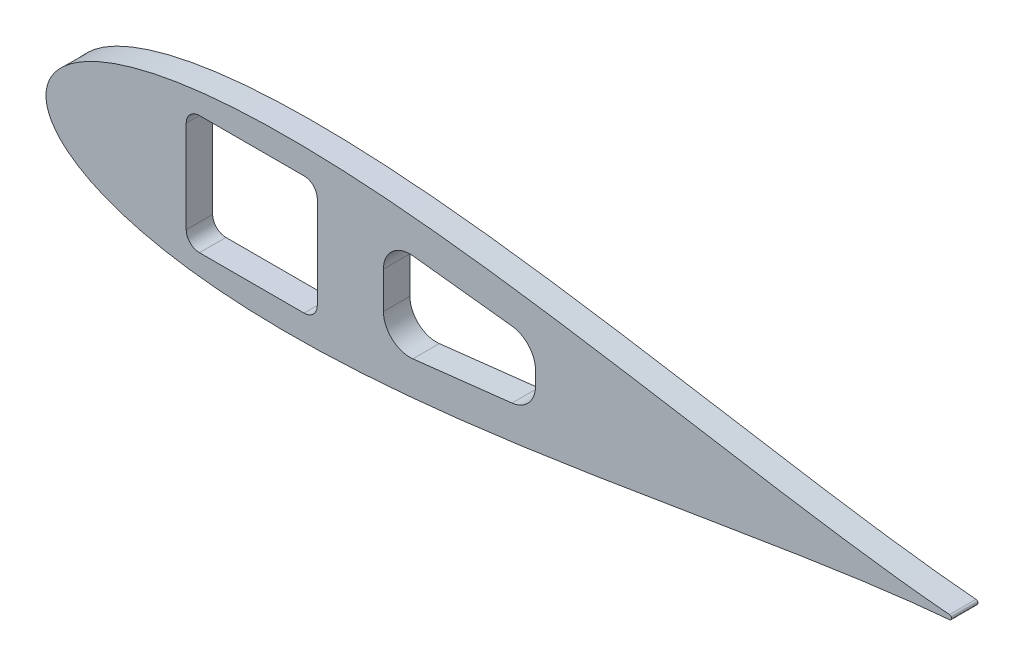
SolidWorks part; units mm, degrees
ref_plane "Front Plane" through (0, 0, 0) normal (0, 0, 1) x (1, 0, 0)
ref_plane "Top Plane" through (0, 0, 0) normal (0, 1, 0) x (1, 0, 0)
ref_plane "Right Plane" through (0, 0, 0) normal (1, 0, 0) x (0, 0, -1)
curve "Curve5"
  spline degree 3 poles (99.3714, -0.0082, 0) (100.2526, 0, 0) (99.3714, 0.0082, 0) (98.8504, 0.035, 0) (97.904, 0.0811, 0) (96.8285, 0.1543, 0) (95.5159, 0.2583, 0) (94.013, 0.3972, 0) (92.313, 0.574, 0) (90.4281, 0.791, 0) (88.3655, 1.0495, 0) (86.1348, 1.3497, 0) (83.7456, 1.691, 0) (81.2082, 2.0715, 0) (78.5335, 2.4886, 0) (75.7326, 2.9386, 0) (72.8172, 3.4168, 0) (69.799, 3.9177, 0) (66.6904, 4.435, 0) (63.5039, 4.9616, 0) (60.2521, 5.4899, 0) (56.948, 6.0119, 0) (53.6049, 6.519, 0) (50.2363, 7.0024, 0) (46.8558, 7.4534, 0) (43.4774, 7.8632, 0) (40.1152, 8.2232, 0) (36.7837, 8.5249, 0) (33.4975, 8.7606, 0) (30.2716, 8.923, 0) (27.1211, 9.0055, 0) (24.0614, 9.0025, 0) (21.108, 8.909, 0) (18.277, 8.7213, 0) (15.5843, 8.4369, 0) (13.0466, 8.0543, 0) (10.6806, 7.5735, 0) (8.5039, 6.996, 0) (6.5349, 6.3253, 0) (4.7933, 5.5673, 0) (3.3001, 4.7321, 0) (2.0777, 3.8366, 0) (1.1467, 2.91, 0) (0.5165, 2.0014, 0) (0.165, 1.1816, 0) (0.0231, 0.524, 0) (-0.0093, 0, 0) (0.0231, -0.524, 0) (0.165, -1.1816, 0) (0.5165, -2.0014, 0) (1.1467, -2.91, 0) (2.0777, -3.8366, 0) (3.3001, -4.7321, 0) (4.7933, -5.5673, 0) (6.5349, -6.3253, 0) (8.5039, -6.996, 0) (10.6806, -7.5735, 0) (13.0466, -8.0543, 0) (15.5843, -8.4369, 0) (18.277, -8.7213, 0) (21.108, -8.909, 0) (24.0614, -9.0025, 0) (27.1211, -9.0055, 0) (30.2716, -8.923, 0) (33.4975, -8.7606, 0) (36.7837, -8.5249, 0) (40.1152, -8.2232, 0) (43.4774, -7.8632, 0) (46.8558, -7.4534, 0) (50.2363, -7.0024, 0) (53.6049, -6.519, 0) (56.948, -6.0119, 0) (60.2521, -5.4899, 0) (63.5039, -4.9616, 0) (66.6904, -4.435, 0) (69.799, -3.9177, 0) (72.8172, -3.4168, 0) (75.7326, -2.9386, 0) (78.5335, -2.4886, 0) (81.2082, -2.0715, 0) (83.7456, -1.691, 0) (86.1348, -1.3497, 0) (88.3655, -1.0495, 0) (90.4281, -0.791, 0) (92.313, -0.574, 0) (94.013, -0.3972, 0) (95.5159, -0.2583, 0) (96.8285, -0.1543, 0) (97.904, -0.0811, 0) (98.8504, -0.035, 0) (99.3714, -0.0082, 0) (100.2526, 0, 0) (99.3714, 0.0082, 0) knots -0.009667 -0.005395 -0.002168 0 0.002168 0.005395 0.009667 0.014967 0.021271 0.028553 0.036781 0.04592 0.055932 0.066773 0.078397 0.090755 0.103793 0.117456 0.131686 0.146422 0.1616 0.177156 0.193024 0.209135 0.225421 0.241812 0.258238 0.274629 0.290914 0.307025 0.322893 0.338448 0.353626 0.368361 0.38259 0.396253 0.40929 0.421647 0.43327 0.444109 0.454119 0.463255 0.471479 0.478755 0.485052 0.490344 0.49461 0.497833 0.5 0.502167 0.50539 0.509656 0.514948 0.521245 0.528521 0.536745 0.545881 0.555891 0.56673 0.578353 0.59071 0.603747 0.61741 0.631639 0.646374 0.661552 0.677107 0.692975 0.709086 0.725371 0.741762 0.758188 0.774579 0.790865 0.806976 0.822844 0.8384 0.853578 0.868314 0.882544 0.896207 0.909245 0.921603 0.933227 0.944068 0.95408 0.963219 0.971447 0.978729 0.985033 0.990333 0.994605 0.997832 1 1.002168 1.005395 1.009667 periodic
sketch "Sketch2" plane through (0, 0, 0) normal (0, 0, 1) x (1, 0, 0)
  line L0 (642.3793, 0) -> (0, 0) construction
  circle A14 centre (642.3793, 0) radius 1.5875 construction
  arc A15 (642.5108, -1.582) -> (642.5108, 1.582) centre (642.3793, 0) ccw
  spline S2 degree 3 poles (666.3448, -0.0547) (672.2538, 0) (666.3448, 0.0547) (662.8509, 0.2344) (656.505, 0.5436) (649.293, 1.0348) (640.4916, 1.7319) (630.4138, 2.6634) (619.0141, 3.8493) (606.375, 5.3044) (592.5439, 7.0376) (577.5855, 9.0506) (561.5643, 11.3389) (544.5497, 13.8907) (526.6141, 16.6877) (507.8326, 19.7051) (488.2827, 22.9117) (468.0444, 26.2704) (447.1994, 29.739) (425.8316, 33.2703) (404.0263, 36.8132) (381.8707, 40.3133) (359.4533, 43.7135) (336.8645, 46.9554) (314.1962, 49.9798) (291.5418, 52.7277) (268.9963, 55.1412) (246.6566, 57.1646) (224.6209, 58.7452) (202.9892, 59.8341) (181.8631, 60.3875) (161.3458, 60.367) (141.542, 59.7399) (122.5581, 58.4818) (104.5023, 56.5743) (87.485, 54.0089) (71.6197, 50.7848) (57.0237, 46.9125) (43.8205, 42.415) (32.1416, 37.3322) (22.1291, 31.7315) (13.9324, 25.7264) (7.6896, 19.5132) (3.4631, 13.4204) (1.1063, 7.9234) (0.1546, 3.5138) (-0.0622, 0) (0.1546, -3.5138) (1.1063, -7.9234) (3.4631, -13.4204) (7.6896, -19.5132) (13.9324, -25.7264) (22.1291, -31.7315) (32.1416, -37.3322) (43.8205, -42.415) (57.0237, -46.9125) (71.6197, -50.7848) (87.485, -54.0089) (104.5023, -56.5743) (122.5581, -58.4818) (141.542, -59.7399) (161.3458, -60.367) (181.8631, -60.3875) (202.9892, -59.8341) (224.6209, -58.7452) (246.6566, -57.1646) (268.9963, -55.1412) (291.5418, -52.7277) (314.1962, -49.9798) (336.8645, -46.9554) (359.4533, -43.7135) (381.8707, -40.3133) (404.0263, -36.8132) (425.8316, -33.2703) (447.1994, -29.739) (468.0444, -26.2704) (488.2827, -22.9117) (507.8326, -19.7051) (526.6141, -16.6877) (544.5497, -13.8907) (561.5643, -11.3389) (577.5855, -9.0506) (592.5439, -7.0376) (606.375, -5.3044) (619.0141, -3.8493) (630.4138, -2.6634) (640.4916, -1.7319) (649.293, -1.0348) (656.505, -0.5436) (662.8509, -0.2344) (666.3448, -0.0547) (672.2538, 0) (666.3448, 0.0547) knots -0.009667 -0.005395 -0.002168 0 0.002168 0.005395 0.009667 0.014967 0.021271 0.028553 0.036781 0.04592 0.055932 0.066773 0.078397 0.090755 0.103793 0.117456 0.131686 0.146422 0.1616 0.177156 0.193024 0.209135 0.225421 0.241812 0.258238 0.274629 0.290914 0.307025 0.322893 0.338448 0.353626 0.368361 0.38259 0.396253 0.40929 0.421647 0.43327 0.444109 0.454119 0.463255 0.471479 0.478755 0.485052 0.490344 0.49461 0.497833 0.5 0.502167 0.50539 0.509656 0.514948 0.521245 0.528521 0.536745 0.545881 0.555891 0.56673 0.578353 0.59071 0.603747 0.61741 0.631639 0.646374 0.661552 0.677107 0.692975 0.709086 0.725371 0.741762 0.758188 0.774579 0.790865 0.806976 0.822844 0.8384 0.853578 0.868314 0.882544 0.896207 0.909245 0.921603 0.933227 0.944068 0.95408 0.963219 0.971447 0.978729 0.985033 0.990333 0.994605 0.997832 1 1.002168 1.005395 1.009667 only from (670.56, 0) to (670.56, 0)
  point P8 (1.2169, -4.6585)
  point P10 (1.2169, 4.6585)
  dimension "D10" = 3.175
extrude "Boss-Extrude1" add sketch "Sketch2" along normal blind 5.4737
extrude "Cut-Extrude4" cut sketch "Sketch7" against normal through all
sketch "Sketch7" plane through (327.9592, -13.7514, 6.35) normal (0, 0, 1) x (1, 0, 0)
  line L1 (-154.9852, -16.7286) -> (-66.0852, -16.7286)
  line L2 (-154.9852, -16.7286) -> (-154.9852, 44.2314)
  line L3 (-154.9852, 44.2314) -> (-66.0852, 44.2314)
  line L4 (-66.0852, -16.7286) -> (-66.0852, 44.2314)
  line L5 (-154.9852, -16.7286) -> (-66.0852, 44.2314) construction
  line L6 (-154.9852, 44.2314) -> (-66.0852, -16.7286) construction
  point P0 (-110.5352, 13.7514)
extrude "Cut-Extrude5" cut sketch "Sketch8" against normal through all
sketch "Sketch8" plane through (327.9592, -13.7514, 6.35) normal (0, 0, 1) x (1, 0, 0)
  circle A0 centre (314.9285, 13.7514) radius 1.2446
scale "Scale1" scale about origin uniform scaling yes scale factor 0.27
sketch "Sketch11" plane through (0, 0, 0) normal (0, 0, -1) x (-1, 0, 0)
  arc A1 (-173.4779, 0.4272) -> (-173.4779, -0.4272) centre (-173.4424, 0) ccw
  arc A2 (-173.4779, 0.4272) -> (-173.4779, -0.4272) centre (-173.4424, 0) ccw
  spline S1 degree 3 poles (2815.5695, -253.5529) (-280.9838, -9.1615) (-219.9614, 3.8791) (-170.2117, -0.7191) (-167.1338, -1.0393) (-163.7212, -1.4322) (-159.9869, -1.9002) (-155.9481, -2.4437) (-151.6224, -3.0615) (-147.0284, -3.7505) (-142.1858, -4.5057) (-137.1148, -5.3204) (-131.8363, -6.1862) (-126.372, -7.093) (-120.7438, -8.0295) (-114.9745, -8.983) (-109.0871, -9.9396) (-103.1051, -10.8846) (-97.0524, -11.8026) (-90.9534, -12.678) (-84.833, -13.4946) (-78.7163, -14.2365) (-72.629, -14.8881) (-66.5973, -15.4344) (-60.6476, -15.8612) (-54.8071, -16.1552) (-49.103, -16.3046) (-43.5634, -16.2991) (-38.2163, -16.1298) (-33.0907, -15.7901) (-28.2156, -15.2751) (-23.621, -14.5824) (-19.3373, -13.7119) (-15.3964, -12.6664) (-11.8315, -11.4521) (-8.6782, -10.0797) (-5.9749, -8.5675) (-3.7618, -6.9461) (-2.0762, -5.2686) (-0.935, -3.6235) (-0.2987, -2.1393) (-0.0417, -0.9487) (0.0168, 0) (-0.0417, 0.9487) (-0.2987, 2.1393) (-0.935, 3.6235) (-2.0762, 5.2686) (-3.7618, 6.9461) (-5.9749, 8.5675) (-8.6782, 10.0797) (-11.8315, 11.4521) (-15.3964, 12.6664) (-19.3373, 13.7119) (-23.621, 14.5824) (-28.2156, 15.2751) (-33.0907, 15.7901) (-38.2163, 16.1298) (-43.5634, 16.2991) (-49.103, 16.3046) (-54.8071, 16.1552) (-60.6476, 15.8612) (-66.5973, 15.4344) (-72.629, 14.8881) (-78.7163, 14.2365) (-84.833, 13.4946) (-90.9534, 12.678) (-97.0524, 11.8026) (-103.1051, 10.8846) (-109.0871, 9.9396) (-114.9745, 8.983) (-120.7438, 8.0295) (-126.372, 7.093) (-131.8363, 6.1862) (-137.1148, 5.3204) (-142.1858, 4.5057) (-147.0284, 3.7505) (-151.6224, 3.0615) (-155.9481, 2.4437) (-159.9869, 1.9002) (-163.7212, 1.4322) (-167.1338, 1.0393) (-170.2117, 0.7191) (-219.9604, -3.8791) (-280.9814, 9.1609) (2815.3794, 253.5379) knots -0.362057 -0.362057 -0.362057 -0.362057 0.021271 0.028553 0.036781 0.04592 0.055932 0.066773 0.078397 0.090755 0.103793 0.117456 0.131686 0.146422 0.1616 0.177156 0.193024 0.209135 0.225421 0.241812 0.258238 0.274629 0.290914 0.307025 0.322893 0.338448 0.353626 0.368361 0.38259 0.396253 0.40929 0.421647 0.43327 0.444109 0.454119 0.463255 0.471479 0.478755 0.485052 0.490344 0.49461 0.497833 0.5 0.502167 0.50539 0.509656 0.514948 0.521245 0.528521 0.536745 0.545881 0.555891 0.56673 0.578353 0.59071 0.603747 0.61741 0.631639 0.646374 0.661552 0.677107 0.692975 0.709086 0.725371 0.741762 0.758188 0.774579 0.790865 0.806976 0.822844 0.8384 0.853578 0.868314 0.882544 0.896207 0.909245 0.921603 0.933227 0.944068 0.95408 0.963219 0.971447 0.978729 1.362049 1.362049 1.362049 1.362049 only from (-173.4779, -0.4272) to (-173.4779, 0.4272)
  spline S2 degree 3 poles (-173.4779, -0.4272) (-173.3382, -0.4388) (-172.2853, -0.5275) (-170.2117, -0.7191) (-167.1338, -1.0393) (-163.7212, -1.4322) (-159.9869, -1.9002) (-155.9481, -2.4437) (-151.6224, -3.0615) (-147.0284, -3.7505) (-142.1858, -4.5057) (-137.1148, -5.3204) (-131.8363, -6.1862) (-126.372, -7.093) (-120.7438, -8.0295) (-114.9745, -8.983) (-109.0871, -9.9396) (-103.1051, -10.8846) (-97.0524, -11.8026) (-90.9534, -12.678) (-84.833, -13.4946) (-78.7163, -14.2365) (-72.629, -14.8881) (-66.5973, -15.4344) (-60.6476, -15.8612) (-54.8071, -16.1552) (-49.103, -16.3046) (-43.5634, -16.2991) (-38.2163, -16.1298) (-33.0907, -15.7901) (-28.2156, -15.2751) (-23.621, -14.5824) (-19.3373, -13.7119) (-15.3964, -12.6664) (-11.8315, -11.4521) (-8.6782, -10.0797) (-5.9749, -8.5675) (-3.7618, -6.9461) (-2.0762, -5.2686) (-0.935, -3.6235) (-0.2987, -2.1393) (-0.0417, -0.9487) (0.0168, 0) (-0.0417, 0.9487) (-0.2987, 2.1393) (-0.935, 3.6235) (-2.0762, 5.2686) (-3.7618, 6.9461) (-5.9749, 8.5675) (-8.6782, 10.0797) (-11.8315, 11.4521) (-15.3964, 12.6664) (-19.3373, 13.7119) (-23.621, 14.5824) (-28.2156, 15.2751) (-33.0907, 15.7901) (-38.2163, 16.1298) (-43.5634, 16.2991) (-49.103, 16.3046) (-54.8071, 16.1552) (-60.6476, 15.8612) (-66.5973, 15.4344) (-72.629, 14.8881) (-78.7163, 14.2365) (-84.833, 13.4946) (-90.9534, 12.678) (-97.0524, 11.8026) (-103.1051, 10.8846) (-109.0871, 9.9396) (-114.9745, 8.983) (-120.7438, 8.0295) (-126.372, 7.093) (-131.8363, 6.1862) (-137.1148, 5.3204) (-142.1858, 4.5057) (-147.0284, 3.7505) (-151.6224, 3.0615) (-155.9481, 2.4437) (-159.9869, 1.9002) (-163.7212, 1.4322) (-167.1338, 1.0393) (-170.2117, 0.7191) (-172.2853, 0.5275) (-173.3382, 0.4388) (-173.4779, 0.4272) knots 0.020157 0.020157 0.020157 0.020157 0.021271 0.028553 0.036781 0.04592 0.055932 0.066773 0.078397 0.090755 0.103793 0.117456 0.131686 0.146422 0.1616 0.177156 0.193024 0.209135 0.225421 0.241812 0.258238 0.274629 0.290914 0.307025 0.322893 0.338448 0.353626 0.368361 0.38259 0.396253 0.40929 0.421647 0.43327 0.444109 0.454119 0.463255 0.471479 0.478755 0.485052 0.490344 0.49461 0.497833 0.5 0.502167 0.50539 0.509656 0.514948 0.521245 0.528521 0.536745 0.545881 0.555891 0.56673 0.578353 0.59071 0.603747 0.61741 0.631639 0.646374 0.661552 0.677107 0.692975 0.709086 0.725371 0.741762 0.758188 0.774579 0.790865 0.806976 0.822844 0.8384 0.853578 0.868314 0.882544 0.896207 0.909245 0.921603 0.933227 0.944068 0.95408 0.963219 0.971447 0.978729 0.979843 0.979843 0.979843 0.979843
  dimension "D1" = 0
extrude "Boss-Extrude2" add sketch "Sketch11" against normal blind 5.08
sketch "Sketch10" plane through (0, 0, 0) normal (0, 0, 1) x (1, 0, 0)
  line L1 (26.924, -11.4046) -> (52.0912, -11.4046)
  line L2 (26.924, -11.4046) -> (26.924, 11.4046)
  line L3 (26.924, 11.4046) -> (52.0912, 11.4046)
  line L4 (52.0912, -11.4046) -> (52.0912, 11.4046)
  line L5 (26.924, -11.4046) -> (52.0912, 11.4046) construction
  line L6 (26.924, 11.4046) -> (52.0912, -11.4046) construction
  point P0 (39.5076, 0)
  dimension "D1" = 25.1672
  dimension "D2" = 26.924
  dimension "D5" = 22.8092
extrude "Cut-Extrude6" cut sketch "Sketch10" along normal through all
fillet "Fillet1" radius 2.54 4 edges at (26.924, 11.4046, 2.54) (52.0912, 11.4046, 2.54) (52.0912, -11.4046, 2.54) (26.924, -11.4046, 2.54)
sketch "Sketch12" plane through (0, 0, 0) normal (0, 0, -1) x (-1, 0, 0)
  line L0 (-64.7912, -9.207) -> (-64.7912, 9.207)
  line L1 (-64.7912, 9.207) -> (-93.9782, 5.8915)
  line L2 (-93.9782, 5.8915) -> (-93.9782, -5.8915)
  line L3 (-93.9782, -5.8915) -> (-64.7912, -9.207)
  line L4 (-52.0912, -8.8646) -> (-52.0912, 8.8646) construction
  spline S0 degree 3 poles (-173.4779, 0.4272) (-173.3382, 0.4388) (-172.2853, 0.5275) (-170.2117, 0.7191) (-167.1338, 1.0393) (-163.7212, 1.4322) (-159.9869, 1.9002) (-155.9481, 2.4437) (-151.6224, 3.0615) (-147.0284, 3.7505) (-142.1858, 4.5057) (-137.1148, 5.3204) (-131.8363, 6.1862) (-126.372, 7.093) (-120.7438, 8.0295) (-114.9745, 8.983) (-109.0871, 9.9396) (-103.1051, 10.8846) (-97.0524, 11.8026) (-90.9534, 12.678) (-84.833, 13.4946) (-78.7163, 14.2365) (-72.629, 14.8881) (-66.5973, 15.4344) (-60.6476, 15.8612) (-54.8071, 16.1552) (-49.103, 16.3046) (-43.5634, 16.2991) (-38.2163, 16.1298) (-33.0907, 15.7901) (-28.2156, 15.2751) (-23.621, 14.5824) (-19.3373, 13.7119) (-15.3964, 12.6664) (-11.8315, 11.4521) (-8.6782, 10.0797) (-5.9749, 8.5675) (-3.7618, 6.9461) (-2.0762, 5.2686) (-0.935, 3.6235) (-0.2987, 2.1393) (-0.0417, 0.9487) (0.0168, 0) (-0.0417, -0.9487) (-0.2987, -2.1393) (-0.935, -3.6235) (-2.0762, -5.2686) (-3.7618, -6.9461) (-5.9749, -8.5675) (-8.6782, -10.0797) (-11.8315, -11.4521) (-15.3964, -12.6664) (-19.3373, -13.7119) (-23.621, -14.5824) (-28.2156, -15.2751) (-33.0907, -15.7901) (-38.2163, -16.1298) (-43.5634, -16.2991) (-49.103, -16.3046) (-54.8071, -16.1552) (-60.6476, -15.8612) (-66.5973, -15.4344) (-72.629, -14.8881) (-78.7163, -14.2365) (-84.833, -13.4946) (-90.9534, -12.678) (-97.0524, -11.8026) (-103.1051, -10.8846) (-109.0871, -9.9396) (-114.9745, -8.983) (-120.7438, -8.0295) (-126.372, -7.093) (-131.8363, -6.1862) (-137.1148, -5.3204) (-142.1858, -4.5057) (-147.0284, -3.7505) (-151.6224, -3.0615) (-155.9481, -2.4437) (-159.9869, -1.9002) (-163.7212, -1.4322) (-167.1338, -1.0393) (-170.2117, -0.7191) (-172.2853, -0.5275) (-173.3382, -0.4388) (-173.4779, -0.4272) knots 0.020157 0.020157 0.020157 0.020157 0.021271 0.028553 0.036781 0.04592 0.055932 0.066773 0.078397 0.090755 0.103793 0.117456 0.131686 0.146422 0.1616 0.177156 0.193024 0.209135 0.225421 0.241812 0.258238 0.274629 0.290914 0.307025 0.322893 0.338448 0.353626 0.368361 0.38259 0.396253 0.40929 0.421647 0.43327 0.444109 0.454119 0.463255 0.471479 0.478755 0.485052 0.490344 0.49461 0.497833 0.5 0.502167 0.50539 0.509656 0.514948 0.521245 0.528521 0.536745 0.545881 0.555891 0.56673 0.578353 0.59071 0.603747 0.61741 0.631639 0.646374 0.661552 0.677107 0.692975 0.709086 0.725371 0.741762 0.758188 0.774579 0.790865 0.806976 0.822844 0.8384 0.853578 0.868314 0.882544 0.896207 0.909245 0.921603 0.933227 0.944068 0.95408 0.963219 0.971447 0.978729 0.979843 0.979843 0.979843 0.979843 construction
  point P2 (-64.7912, -15.557)
  point P5 (-93.9782, -12.2415)
  point P8 (-106.6782, -10.3187)
  point P9 (-106.6782, 10.3187)
  point P12 (-64.7912, 0)
  point P13 (-93.9782, 0)
  point P16 (-52.0912, 0)
  dimension "D1" = 6.35
  dimension "D2" = 6.35
  dimension "D3" = 12.7
  dimension "D4" = 20.6375
  dimension "D5" = 12.7
extrude "Cut-Extrude7" cut sketch "Sketch12" against normal through all
fillet "Fillet2" radius 5.08 4 edges at (64.7912, 9.207, 2.54) (64.7912, -9.207, 2.54) (93.9782, 5.8915, 2.54) (93.9782, -5.8915, 2.54)
equation "\"0.5n\"=0"
equation "\"D2@Sketch12\"=\"D1@Sketch12\""
equation "\"D1@Sketch10\"=.898/cos(25deg)"
